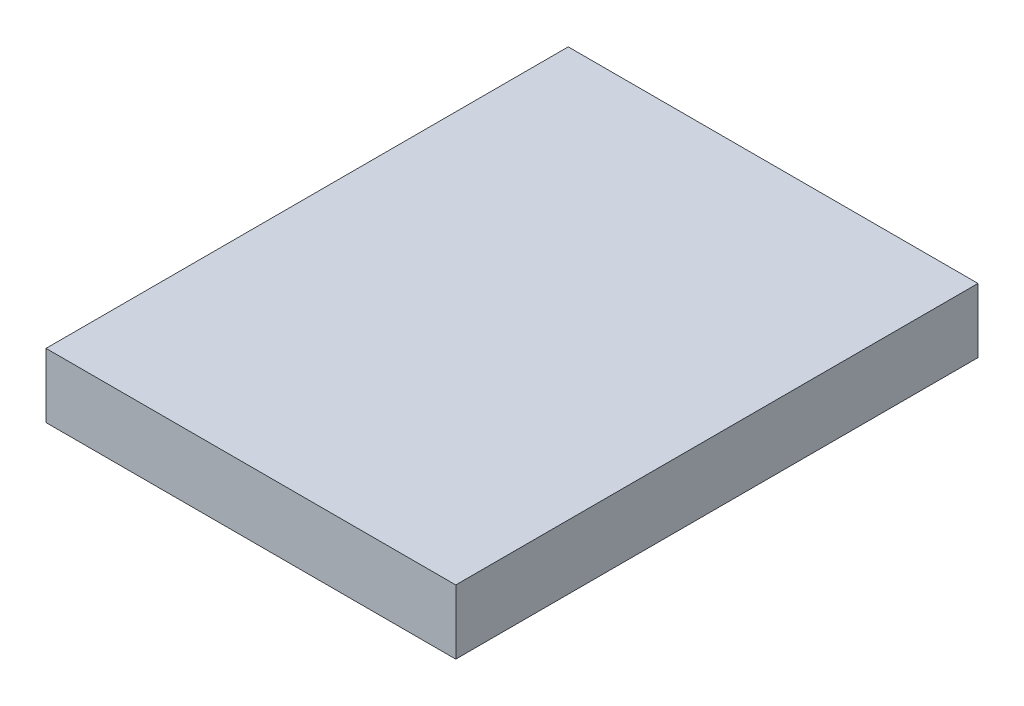
SolidWorks part; units mm, degrees
ref_plane "Front Plane" through (0, 0, 0) normal (0, 0, 1) x (1, 0, 0)
ref_plane "Top Plane" through (0, 0, 0) normal (0, 1, 0) x (1, 0, 0)
ref_plane "Right Plane" through (0, 0, 0) normal (1, 0, 0) x (0, 0, -1)
sketch "Sketch1" plane through (0, 0, 0) normal (0, 1, 0) x (1, 0, 0)
  line L1 (-25.5, -32.5) -> (25.5, -32.5)
  line L2 (-25.5, -32.5) -> (-25.5, 32.5)
  line L3 (-25.5, 32.5) -> (25.5, 32.5)
  line L4 (25.5, -32.5) -> (25.5, 32.5)
  line L5 (-25.5, -32.5) -> (25.5, 32.5) construction
  line L6 (-25.5, 32.5) -> (25.5, -32.5) construction
  point P0 (0, 0)
  dimension "D1" = 51
  dimension "D2" = 65
extrude "Boss-Extrude1" add sketch "Sketch1" along normal blind 8
